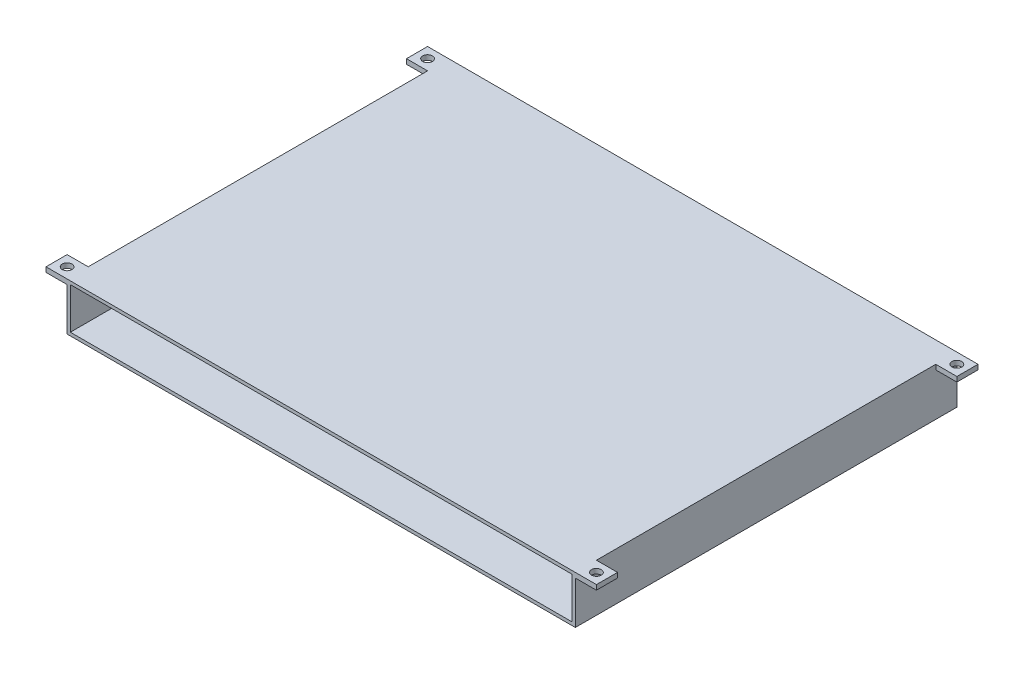
SolidWorks part; units mm, degrees
ref_plane "Płaszczyzna XY" through (0, 0, 0) normal (0, 0, 1) x (1, 0, 0)
ref_plane "Płaszczyzna XZ" through (0, 0, 0) normal (0, 1, 0) x (1, 0, 0)
ref_plane "Płaszczyzna YZ" through (0, 0, 0) normal (1, 0, 0) x (0, 0, -1)
sketch "Sketch2" plane through (-188, 0, 0) normal (-1, 0, 0) x (0, 0, 1)
  line L0 (-59, 12.7) -> (-57, 12.7) construction
  line L1 (-59, 12.7) -> (-57, 12.7)
  line L2 (-59, -12.7) -> (-57, -12.7) construction
  line L3 (-59, -12.7) -> (-57, -12.7)
  line L4 (-233, 9.7) -> (-233, 0) construction
  line L5 (-233, 9.7) -> (-233, 0)
  line L6 (0, -8.2) -> (0, 8.2) construction
  line L7 (0, -8.2) -> (0, 8.2)
  line L8 (-57, 12.7) -> (0, 12.7)
  line L9 (0, 12.7) -> (0, 8.2)
  line L10 (-57, -12.7) -> (0, -12.7)
  line L11 (0, -12.7) -> (0, -8.2)
  line L12 (-59, 12.7) -> (-233, 12.7)
  line L13 (-233, 12.7) -> (-233, 9.7)
  line L14 (-59, -12.7) -> (-233, -12.7)
  line L15 (-233, -12.7) -> (-233, 0)
extrude "Boss-Extrude1" add sketch "Sketch2" along normal blind 2
sketch "Sketch3" plane through (0, 12.7, 0) normal (0, 1, 0) x (1, 0, 0)
  line L0 (-190, 233) -> (-188, 233) construction
  line L1 (-190, 233) -> (-188, 233)
  line L2 (-190, 0) -> (-190, 233) construction
  line L3 (-190, 0) -> (-190, 233)
  line L4 (121, 59) -> (121, 233) construction
  line L5 (121, 59) -> (121, 233)
  line L6 (-190, 0) -> (111, 0)
  line L8 (121, 233) -> (-188, 233)
  line L9 (121, 59) -> (121, 0)
  line L10 (121, 0) -> (111, 0)
  line L11 (-188, 0) -> (-188, 233) construction
  dimension "D1" = 299
extrude "Boss-Extrude2" add sketch "Sketch3" along normal blind 2
sketch "Sketch4" plane through (0, 0, -233) normal (0, 0, -1) x (-1, 0, 0)
  line L0 (-121, 14.7) -> (190, 14.7) construction
  line L1 (-121, 14.7) -> (190, 14.7)
  line L2 (190, 14.7) -> (190, -12.7) construction
  line L3 (190, 14.7) -> (190, -12.7)
  line L5 (-111, -12.7) -> (190, -12.7)
  line L6 (-121, 14.7) -> (-121, 12.7) construction
  line L7 (-121, 14.7) -> (-121, 12.7)
  line L8 (-121, 12.7) -> (-121, -12.7)
  line L9 (-121, -12.7) -> (-111, -12.7)
  line L10 (188, 12.7) -> (188, -12.7) construction
  dimension "D1" = 299
extrude "Boss-Extrude3" add sketch "Sketch4" along normal blind 2
sketch "Sketch5" plane through (0, 0, -233) normal (0, 0, -1) x (-1, 0, 0)
  line L0 (27, 0) -> (27, -9.7) construction
  line L1 (27, 9.7) -> (27, 0) construction
  line L2 (37, -9.7) -> (37, 0) construction
  line L3 (37, 0) -> (37, 9.7) construction
  line L4 (27, 0) -> (27, -9.7)
  line L5 (27, 9.7) -> (27, 0)
  line L6 (37, -9.7) -> (37, 0)
  line L7 (37, 0) -> (37, 9.7)
  line L8 (37, 9.7) -> (27, 9.7)
  line L9 (37, -9.7) -> (27, -9.7)
extrude "Boss-Extrude4" add sketch "Sketch5" against normal blind 200 separate body
sketch "Sketch6" plane through (121, 0, 0) normal (1, 0, 0) x (0, 0, -1)
  line L0 (235, 14.7) -> (235, -12.7) construction
  line L1 (235, 14.7) -> (235, -12.7)
  line L2 (0, 14.7) -> (235, 14.7) construction
  line L3 (0, 14.7) -> (235, 14.7)
  line L6 (0, -12.7) -> (0, 12.7) construction
  line L7 (0, -12.7) -> (0, 12.7)
  line L8 (235, -12.7) -> (0, -12.7)
  line L9 (0, 12.7) -> (0, 14.7)
extrude "Boss-Extrude5" add sketch "Sketch6" along normal blind 2 contours L7 L9 L3 L1 L8
sketch "Sketch7" plane through (0, -12.7, 0) normal (0, -1, 0) x (1, 0, 0)
  line L0 (123, -235) -> (123, 0) construction
  line L1 (123, -235) -> (123, 0)
  line L2 (123, -235) -> (-190, -235) construction
  line L3 (123, -235) -> (-190, -235)
  line L4 (-190, -235) -> (-190, 0) construction
  line L5 (-190, -235) -> (-190, 0)
  line L6 (-190, 0) -> (123, 0)
extrude "Boss-Extrude6" add sketch "Sketch7" along normal blind 2
sketch "Sketch8" plane through (123, 0, 0) normal (1, 0, 0) x (0, 0, -1)
  line L6 (117.5, 14.7) -> (117.5, -14.7) construction
  line L11 (0, -14.7) -> (0, 14.7) construction
  line L12 (0, 14.7) -> (235, 14.7) construction
  line L13 (0, 11.7) -> (0, 14.7)
  line L14 (0, 14.7) -> (13, 14.7)
  line L15 (13, 14.7) -> (13, 11.7)
  line L16 (13, 11.7) -> (0, 11.7)
  line L18 (222, 11.7) -> (235, 11.7)
  line L19 (222, 14.7) -> (222, 11.7)
  line L20 (235, 14.7) -> (222, 14.7)
  line L21 (235, 11.7) -> (235, 14.7)
  dimension "D1" = 3
  dimension "D2" = 13
  dimension "D3" = 117.5
extrude "Boss-Extrude10" add sketch "Sketch8" along normal blind 13
ref_plane "Plane1" through (-33.5, 0, 0) normal (-1, 0, 0) x (0, 0, 1)
mirror "Mirror1" about plane through (-33.5, 0, 0) normal (-1, 0, 0) of "Boss-Extrude10"
sketch "Sketch9" plane through (0, 11.7, 0) normal (0, -1, 0) x (1, 0, 0)
  line L0 (123, -235) -> (136, -222) construction
  line L1 (123, -13) -> (136, 0) construction
  circle A0 centre (129.5, -228.5) radius 3
  circle A1 centre (129.5, -6.5) radius 3
  point P12 (129.5, -228.5)
  point P18 (129.5, -6.5)
  dimension "D1" = 6
  dimension "D2" = 6
extrude "Cut-Extrude1" cut sketch "Sketch9" against normal blind 10
mirror "Mirror2" about plane through (-33.5, 0, 0) normal (-1, 0, 0) of "Cut-Extrude1"
